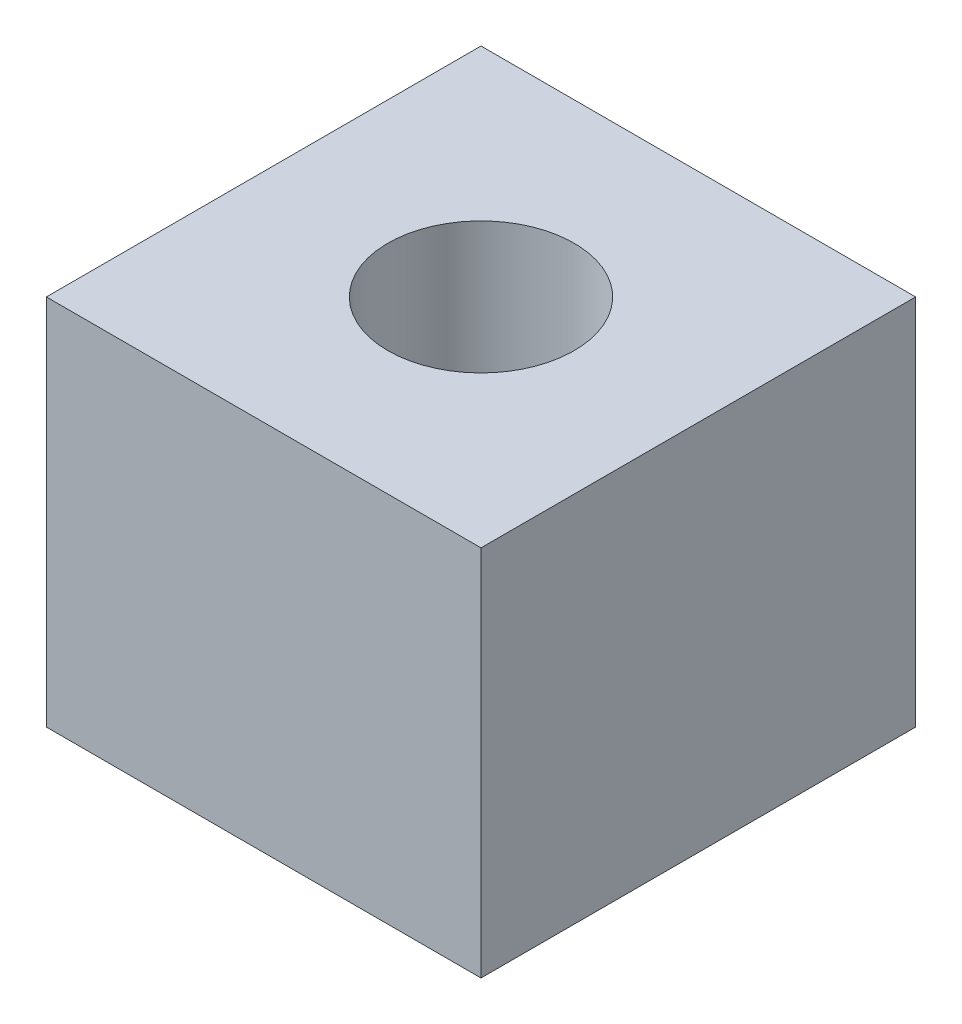
SolidWorks part; units mm, degrees
ref_plane "Front Plane" through (0, 0, 0) normal (0, 0, 1) x (1, 0, 0)
ref_plane "Top Plane" through (0, 0, 0) normal (0, 1, 0) x (1, 0, 0)
ref_plane "Right Plane" through (0, 0, 0) normal (1, 0, 0) x (0, 0, -1)
sketch "Sketch1" plane through (0, 0, 0) normal (0, 1, 0) x (1, 0, 0)
  line L1 (-17.5, 17.5) -> (17.5, 17.5)
  line L2 (-17.5, 17.5) -> (-17.5, -17.5)
  line L3 (-17.5, -17.5) -> (17.5, -17.5)
  line L4 (17.5, 17.5) -> (17.5, -17.5)
  line L5 (-17.5, 17.5) -> (17.5, -17.5) construction
  line L6 (-17.5, -17.5) -> (17.5, 17.5) construction
  point P1 (0, 0)
  dimension "D1" = 35
  dimension "D2" = 35
extrude "Boss-Extrude1" add sketch "Sketch1" along normal blind 30
sketch "Sketch2" plane through (0, 30, 0) normal (0, 1, 0) x (1, 0, 0)
  circle A0 centre (0, 0) radius 7.5
  dimension "D1" = 15
extrude "Cut-Extrude1" cut sketch "Sketch2" against normal blind 20
